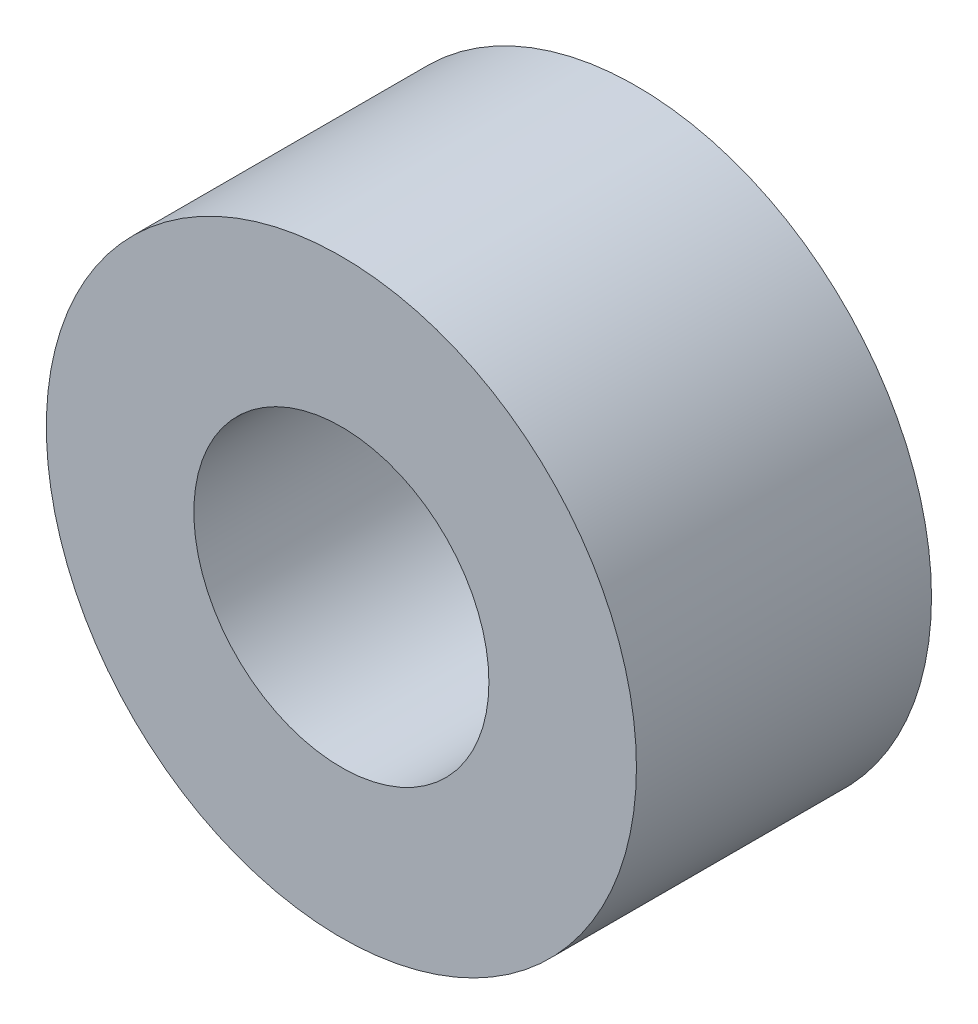
SolidWorks part; units mm, degrees
material "A-Glass Fiber"
ref_plane "Front Plane" through (0, 0, 0) normal (0, 0, 1) x (1, 0, 0)
ref_plane "Top Plane" through (0, 0, 0) normal (0, 1, 0) x (1, 0, 0)
ref_plane "Right Plane" through (0, 0, 0) normal (1, 0, 0) x (0, 0, -1)
sketch "Sketch1" plane through (0, 0, 0) normal (0, 0, 1) x (1, 0, 0)
  circle A0 centre (0, 0) radius 3.175
  circle A1 centre (0, 0) radius 1.5875
  dimension "D1" = 6.35
  dimension "ID" = 3.175
extrude "Extrude1" add sketch "Sketch1" along normal mid plane 3.175
sketch "Sketch2" plane through (0, 0, 0) normal (1, 0, 0) x (0, 0, -1)
  line L0 (-1.5875, -1.5875) -> (1.5875, -1.5875) construction
  line L3 (1.5875, 1.5875) -> (-1.5875, 1.5875) construction
  line L5 (-1.5875, -1.5875) -> (1.5875, -1.5875)
  line L6 (1.5875, 1.5875) -> (-1.5875, 1.5875)
sketch "Sketch4" plane through (0, 0, 1.5875) normal (0, 0, 1) x (1, 0, 0)
  line L0 (0, 0) -> (-1.1225, 1.1225)
  line L1 (0, -48.895) -> (0, 48.895) construction
  circle A0 centre (0, 0) radius 1.5875 construction
  dimension "D1" = 45
